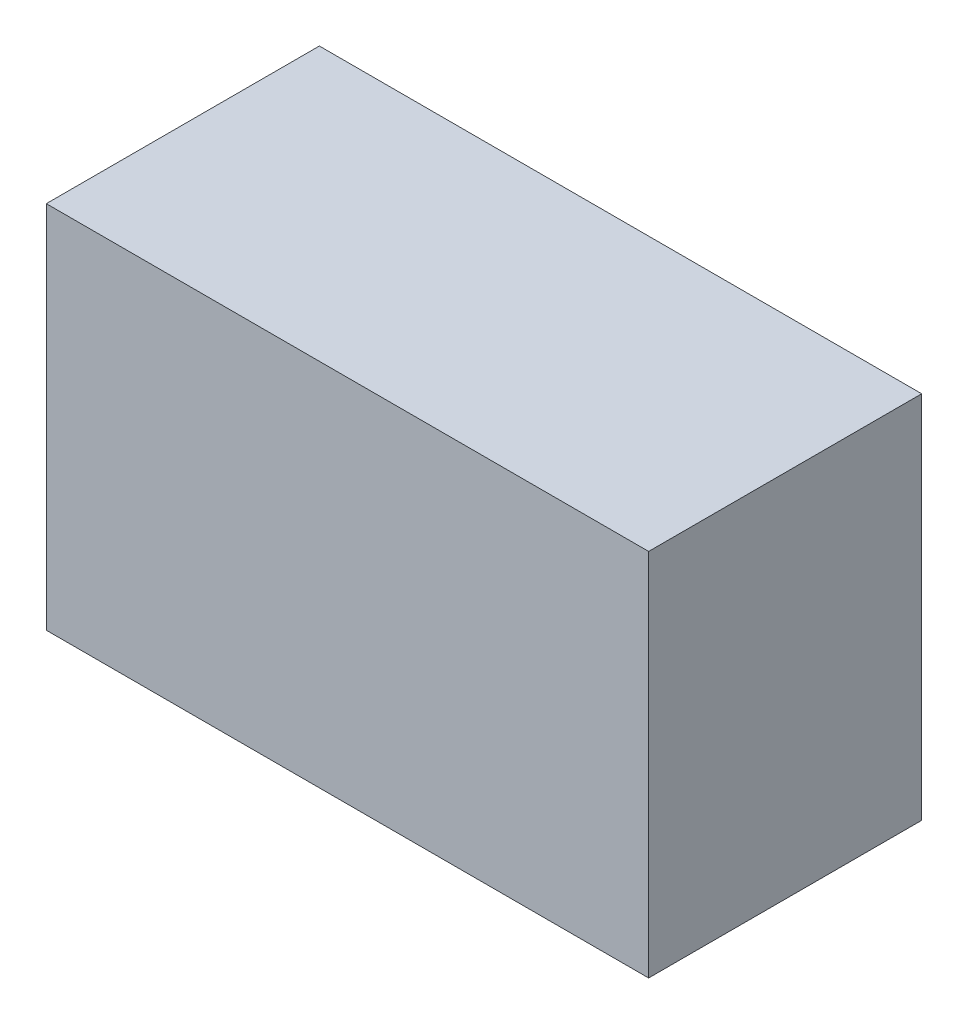
SolidWorks part; units mm, degrees
ref_plane "前视基准面" through (0, 0, 0) normal (0, 0, 1) x (1, 0, 0)
ref_plane "上视基准面" through (0, 0, 0) normal (0, 1, 0) x (1, 0, 0)
ref_plane "右视基准面" through (0, 0, 0) normal (1, 0, 0) x (0, 0, -1)
sketch "草图2" plane through (0, 0, 0) normal (0, 1, 0) x (1, 0, 0)
  line L1 (-37.5, -17) -> (37.5, -17)
  line L2 (-37.5, -17) -> (-37.5, 17)
  line L3 (-37.5, 17) -> (37.5, 17)
  line L4 (37.5, -17) -> (37.5, 17)
  line L5 (-37.5, -17) -> (37.5, 17) construction
  line L6 (-37.5, 17) -> (37.5, -17) construction
  point P0 (0, 0)
  dimension "D1" = 75
  dimension "D2" = 34
extrude "凸台-拉伸1" add sketch "草图2" along normal blind 46
sketch "草图3" plane through (-37.5, 0, 0) normal (-1, 0, 0) x (0, 0, 1)
  line L1 (-15.5418, 8.0844) -> (-9.3383, 8.0844)
  line L2 (-15.5418, 8.0844) -> (-15.5418, -9.5363)
  line L3 (-15.5418, -9.5363) -> (-9.3383, -9.5363)
  line L4 (-9.3383, 8.0844) -> (-9.3383, -9.5363)
extrude "凸台-拉伸2" [suppressed] add sketch "草图3" along normal blind 8
